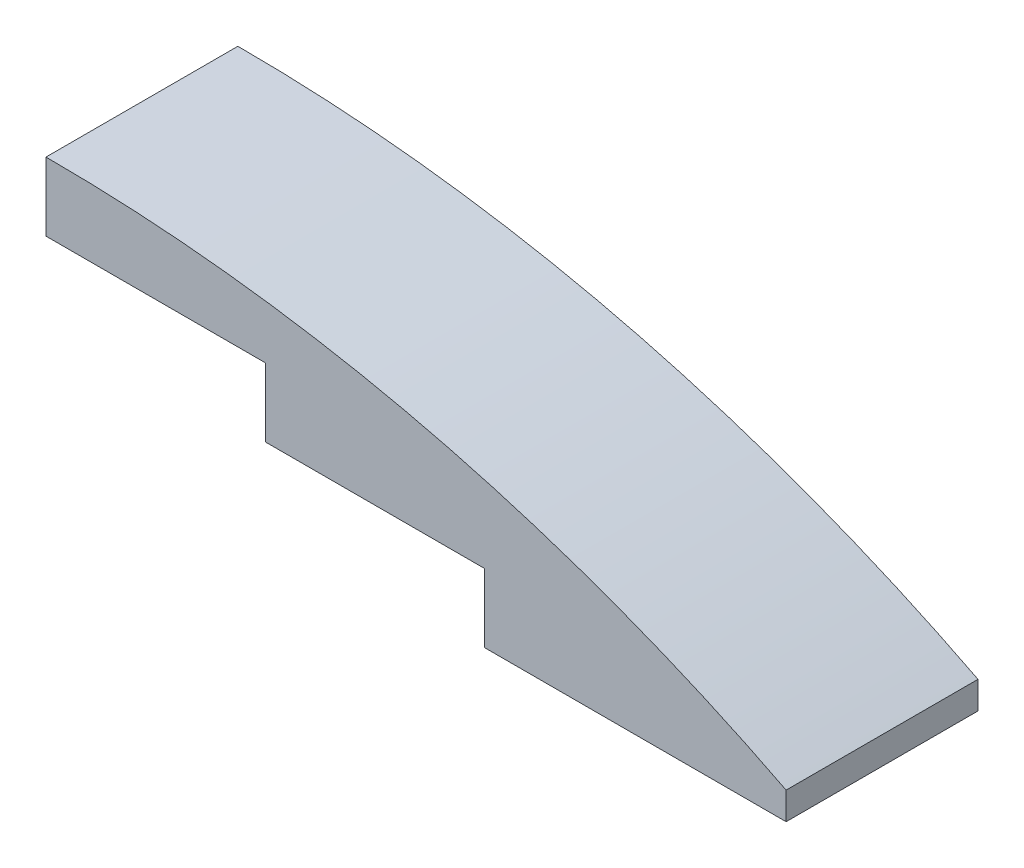
SolidWorks part; units mm, degrees
material "ABS"
ref_plane "Front Plane" through (0, 0, 0) normal (0, 0, 1) x (1, 0, 0)
ref_plane "Top Plane" through (0, 0, 0) normal (0, 1, 0) x (1, 0, 0)
ref_plane "Right Plane" through (0, 0, 0) normal (1, 0, 0) x (0, 0, -1)
sketch "Sketch1" plane through (0, 0, 0) normal (0, 0, 1) x (1, 0, 0)
  line L0 (0, 0) -> (0, -3.175)
  line L1 (0, -3.175) -> (10.16, -3.175)
  line L2 (10.16, -3.175) -> (10.16, -6.35)
  line L3 (10.16, -6.35) -> (20.32, -6.35)
  line L4 (20.32, -6.35) -> (20.32, -9.525)
  line L5 (20.32, -9.525) -> (34.29, -9.525)
  line L6 (34.29, -9.525) -> (34.29, -8.255)
  arc A0 (0, 0) -> (34.29, -8.255) centre (0, -75.3452) cw
  point P3 (34.29, -8.89)
  point P10 (20.32, -7.9375)
  dimension "D1" = 34.29
  dimension "D2" = 20.32
  dimension "D3" = 10.16
  dimension "D4" = 3.175
  dimension "D5" = 3.175
  dimension "D6" = 3.175
  dimension "D7" = 1.27
extrude "Boss-Extrude1" add sketch "Sketch1" along normal mid plane 8.89
sketch "Sketch2" plane through (0, -3.175, 0) normal (0, -1, 0) x (1, 0, 0)
  line L0 (0.3175, -4.1275) -> (10.16, -4.1275)
  line L2 (10.16, 4.1275) -> (0.3175, 4.1275)
  line L3 (0.3175, 4.1275) -> (0.3175, -4.1275)
  line L4 (0, -4.445) -> (10.16, -4.445)
  line L5 (10.16, -4.445) -> (10.16, 4.445)
  line L6 (10.16, 4.445) -> (0, 4.445)
  line L7 (0, 4.445) -> (0, -4.445)
  line L8 (0, -4.445) -> (10.16, -4.445)
  line L9 (10.16, -4.445) -> (10.16, 4.445)
  line L10 (10.16, 4.445) -> (0, 4.445)
  line L11 (0, 4.445) -> (0, -4.445)
  line L12 (9.8425, -4.1275) -> (9.8425, 4.1275) construction
  line L13 (9.8425, 4.1275) -> (0.3175, 4.1275) construction
  line L14 (0.3175, -4.1275) -> (9.8425, -4.1275) construction
  line M7 (10.16, -4.445) -> (10.16, 4.445)
  dimension "D1" = 0
  dimension "D2" = 0.3175
extrude "Cut-Extrude2" cut sketch "Sketch2" against normal offset from surface (1.2049 mm away) 1.27 contours L2 L3 L0 M7
sketch "Sketch3" plane through (0, -6.35, 0) normal (0, -1, 0) x (1, 0, 0)
  line L0 (10.4775, -4.1275) -> (20.32, -4.1275)
  line L2 (20.32, 4.1275) -> (10.4775, 4.1275)
  line L3 (10.4775, 4.1275) -> (10.4775, -4.1275)
  line L4 (10.16, -4.445) -> (20.32, -4.445)
  line L5 (20.32, -4.445) -> (20.32, 4.445)
  line L6 (20.32, 4.445) -> (10.16, 4.445)
  line L7 (10.16, 4.445) -> (10.16, -4.445)
  line L8 (10.16, -4.445) -> (20.32, -4.445)
  line L9 (20.32, -4.445) -> (20.32, 4.445)
  line L10 (20.32, 4.445) -> (10.16, 4.445)
  line L11 (10.16, 4.445) -> (10.16, -4.445)
  line L12 (20.0025, -4.1275) -> (20.0025, 4.1275) construction
  line L13 (20.0025, 4.1275) -> (10.4775, 4.1275) construction
  line L14 (10.4775, -4.1275) -> (20.0025, -4.1275) construction
  line M6 (20.32, -4.445) -> (20.32, 4.445)
  dimension "D1" = 0
  dimension "D2" = 0.3175
extrude "Cut-Extrude3" cut sketch "Sketch3" against normal offset from surface (2.2384 mm away) 1.27 contours L2 L3 L0 M6
sketch "Sketch4" plane through (0, -9.525, 0) normal (0, -1, 0) x (1, 0, 0)
  line L0 (20.6375, -4.1275) -> (33.9725, -4.1275)
  line L1 (33.9725, -4.1275) -> (33.9725, 4.1275)
  line L2 (33.9725, 4.1275) -> (20.6375, 4.1275)
  line L3 (20.6375, 4.1275) -> (20.6375, -4.1275)
  line L4 (20.32, -4.445) -> (34.29, -4.445)
  line L5 (34.29, -4.445) -> (34.29, 4.445)
  line L6 (34.29, 4.445) -> (20.32, 4.445)
  line L7 (20.32, 4.445) -> (20.32, -4.445)
  line L8 (20.32, -4.445) -> (34.29, -4.445)
  line L9 (34.29, -4.445) -> (34.29, 4.445)
  line L10 (34.29, 4.445) -> (20.32, 4.445)
  line L11 (20.32, 4.445) -> (20.32, -4.445)
  dimension "D1" = 0
  dimension "D2" = 0.3175
extrude "Cut-Extrude5" cut sketch "Sketch4" against normal offset from surface (0.1613 mm away) 1.27 contours L2 L3 L0 L1
ref_plane "Plane1" through (0, -11.43, 0) normal (0, 1, 0) x (1, 0, 0)
sketch "Sketch5" plane through (0, -11.43, 0) normal (0, 1, 0) x (1, 0, 0)
  line L0 (34.29, -4.445) -> (20.32, 4.445) construction
  line L1 (20.32, -4.445) -> (20.32, 4.445) construction
  line L2 (20.32, 4.445) -> (10.16, -4.445) construction
  line L3 (10.16, -4.445) -> (0, 4.445) construction
  circle A0 centre (27.305, 0) radius 2.54
  circle A1 centre (15.24, 0) radius 2.54
  circle A2 centre (5.08, 0) radius 2.54
  circle A3 centre (5.08, 0) radius 1.905
  circle A4 centre (15.24, 0) radius 1.905
  circle A5 centre (27.305, 0) radius 1.905
  dimension "D1" = 5.08
  dimension "D2" = 5.08
  dimension "D3" = 5.08
  dimension "D4" = 3.81
  dimension "D5" = 3.81
  dimension "D6" = 3.81
extrude "Boss-Extrude2" [suppressed] add sketch "Sketch5" along normal up to surface (4.9439 mm away)
sketch "Sketch6" plane through (0, 0, 0) normal (0, 0, 1) x (1, 0, 0)
  line L0 (4.8895, -11.43) -> (-4.8895, -11.43) construction
  line L1 (0, -11.43) -> (8.5137, -11.43)
  line L2 (0, -11.43) -> (0, -5.08)
  line L3 (0, -5.08) -> (8.5137, -5.08)
  line L4 (8.5137, -11.43) -> (8.5137, -5.08)
  line L5 (0, -3.175) -> (10.16, -3.175) construction
  line L6 (11.2684, -11.43) -> (18.6142, -11.43)
  line L7 (11.2684, -11.43) -> (11.2684, -8.255)
  line L8 (11.2684, -8.255) -> (18.6142, -8.255)
  line L9 (18.6142, -11.43) -> (18.6142, -8.255)
  line L10 (10.16, -6.35) -> (20.32, -6.35) construction
  dimension "D1" = 1.905
  dimension "D2" = 1.905
extrude "Cut-Extrude6" [suppressed] cut sketch "Sketch6" against normal through all both and the other way through all
